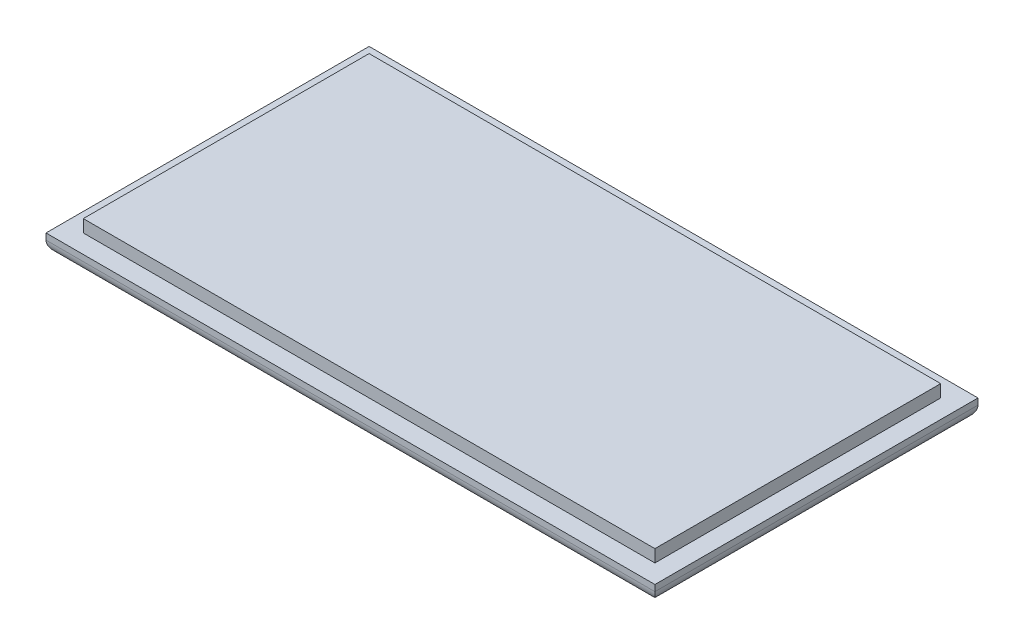
SolidWorks part; units mm, degrees
ref_plane "前视基准面" through (0, 0, 0) normal (0, 0, 1) x (1, 0, 0)
ref_plane "上视基准面" through (0, 0, 0) normal (0, 1, 0) x (1, 0, 0)
ref_plane "右视基准面" through (0, 0, 0) normal (1, 0, 0) x (0, 0, -1)
other "Configuration Table"
sketch "草图1" plane through (0, 0, 0) normal (0, 1, 0) x (1, 0, 0)
  line L1 (-23, 11.5) -> (23, 11.5) construction
  line L2 (-23, 11.5) -> (-23, -11.5) construction
  line L3 (-23, -11.5) -> (23, -11.5) construction
  line L4 (23, 11.5) -> (23, -11.5) construction
  line L5 (-23, 11.5) -> (23, -11.5) construction
  line L6 (-23, -11.5) -> (23, 11.5) construction
  line L7 (-24.5, 13) -> (24.5, 13)
  line L8 (-24.5, 13) -> (-24.5, -13)
  line L9 (-24.5, -13) -> (24.5, -13)
  line L10 (24.5, 13) -> (24.5, -13)
  line L11 (-24.5, 13) -> (24.5, -13) construction
  line L12 (-24.5, -13) -> (24.5, 13) construction
  point P0 (0, 0)
  point P6 (0, 0)
  dimension "D1" = 46
  dimension "D2" = 23
  dimension "D3" = 1.5
  dimension "D4" = 1.5
extrude "凸台-拉伸1" add sketch "草图1" along normal blind 1.5
ref_plane "基准面1" through (0, 1.5, 0) normal (0, 1, 0) x (1, 0, 0)
sketch "草图2" plane through (0, 1.5, 0) normal (0, 1, 0) x (1, 0, 0)
  line L0 (23, 11.5) -> (23, -11.5) construction
  line L1 (-23, -11.5) -> (23, -11.5) construction
  line L2 (-23, 11.5) -> (-23, -11.5) construction
  line L3 (-23, 11.5) -> (23, 11.5) construction
  line L4 (23, 11.5) -> (23, -11.5)
  line L5 (-23, -11.5) -> (23, -11.5)
  line L6 (-23, 11.5) -> (-23, -11.5)
  line L7 (-23, 11.5) -> (23, 11.5)
extrude "凸台-拉伸2" add sketch "草图2" along normal blind 1
fillet "圆角1" radius 1 4 edges at (0, 0, -13) (-24.5, 0, 0) (0, 0, 13) (24.5, 0, 0)
